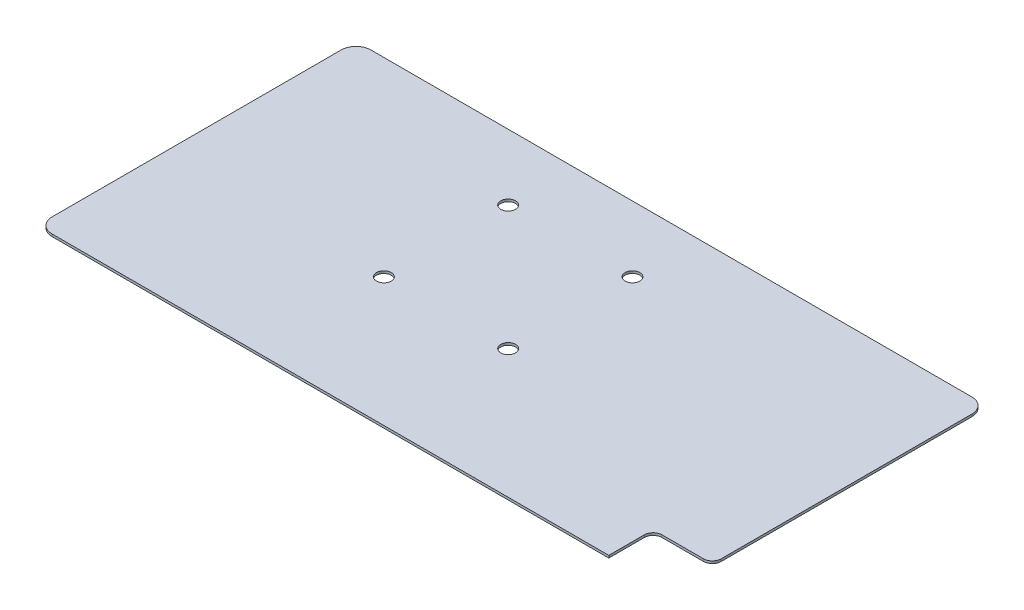
SolidWorks part; units mm, degrees
ref_plane "Front Plane" through (0, 0, 0) normal (0, 0, 1) x (1, 0, 0)
ref_plane "Top Plane" through (0, 0, 0) normal (0, 1, 0) x (1, 0, 0)
ref_plane "Right Plane" through (0, 0, 0) normal (1, 0, 0) x (0, 0, -1)
sketch "Sketch1" plane through (0, 0, 0) normal (0, 1, 0) x (1, 0, 0)
  line L0 (5, 0) -> (208.1, 0)
  line L1 (213.1, -5) -> (213.1, -82.7)
  line L2 (0, -5) -> (0, -102.7)
  line L3 (5, -107.7) -> (188.1, -107.7)
  line L5 (193.1, -95.7) -> (193.1, -102.7)
  line L6 (213.1, -82.7) -> (213.1, -87.7)
  line L7 (31.2359, -64.2) -> (40.6036, -64.2) construction
  line L8 (28.8184, -22.2) -> (44.2298, -22.2) construction
  line L9 (115.6, -36.1114) -> (115.6, -47.2923) construction
  line L10 (73.6, -40.342) -> (73.6, -8.3104) construction
  line L14 (193.1, -102.7) -> (193.1, -107.7)
  line L15 (193.1, -107.7) -> (188.1, -107.7)
  line L16 (196.1, -92.7) -> (210.1, -92.7)
  line L17 (213.1, -89.7) -> (213.1, -87.7)
  circle A0 centre (73.6, -22.2) radius 2.5
  circle A1 centre (115.6, -22.2) radius 2.5
  circle A2 centre (115.6, -64.2) radius 2.5
  circle A3 centre (73.6, -64.2) radius 2.5
  arc A7 (208.1, 0) -> (213.1, -5) centre (208.1, -5) cw
  arc A8 (0, -102.7) -> (5, -107.7) centre (5, -102.7) ccw
  arc A9 (5, 0) -> (0, -5) centre (5, -5) ccw
  arc A10 (193.1, -95.7) -> (196.1, -92.7) centre (196.1, -95.7) cw
  arc A11 (210.1, -92.7) -> (213.1, -89.7) centre (210.1, -89.7) ccw
  point P31 (213.1, 0)
  point P34 (0, -107.7)
  point P37 (0, 0)
  dimension "D1" = 5
  dimension "D3" = 5
  dimension "D4" = 5
  dimension "D5" = 5
  dimension "D7" = 3
  dimension "D2" = 107.7
  dimension "D6" = 213.1
extrude "Boss-Extrude1" add sketch "Sketch1" along normal blind 0.8
